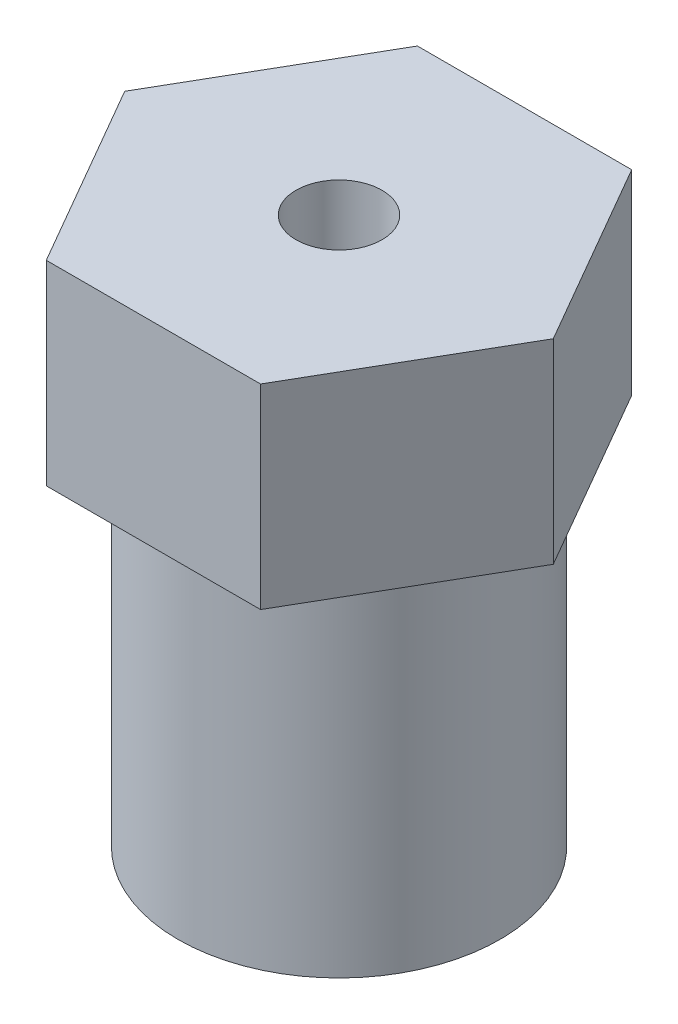
SolidWorks part; units mm, degrees
ref_plane "Front" through (0, 0, 0) normal (0, 0, 1) x (1, 0, 0)
ref_plane "Top" through (0, 0, 0) normal (0, 1, 0) x (1, 0, 0)
ref_plane "Right" through (0, 0, 0) normal (1, 0, 0) x (0, 0, -1)
sketch "Sketch1" plane through (0, 0, 0) normal (0, 1, 0) x (1, 0, 0)
  circle A0 centre (0, 0) radius 5.2324
  dimension "D1" = 10.4648
extrude "Boss-Extrude1" add sketch "Sketch1" along normal blind 11.43
sketch "Sketch2" plane through (0, 11.43, 0) normal (0, 1, 0) x (1, 0, 0)
  line L1 (6.9657, 0) -> (3.4829, 6.0325)
  line L2 (3.4829, 6.0325) -> (-3.4829, 6.0325)
  line L3 (-3.4829, 6.0325) -> (-6.9657, 0)
  line L4 (-6.9657, 0) -> (-3.4829, -6.0325)
  line L5 (-3.4829, -6.0325) -> (3.4829, -6.0325)
  line L6 (3.4829, -6.0325) -> (6.9657, 0)
  circle A0 centre (0, 0) radius 6.0325 construction
  dimension "D1" = 12.065
extrude "Boss-Extrude2" add sketch "Sketch2" along normal blind 6.35
sketch "Sketch3" plane through (0, 17.78, 0) normal (0, 1, 0) x (1, 0, 0)
  circle A0 centre (0, 0) radius 1.397
  dimension "D1" = 2.794
extrude "Cut-Extrude1" cut sketch "Sketch3" against normal through all
